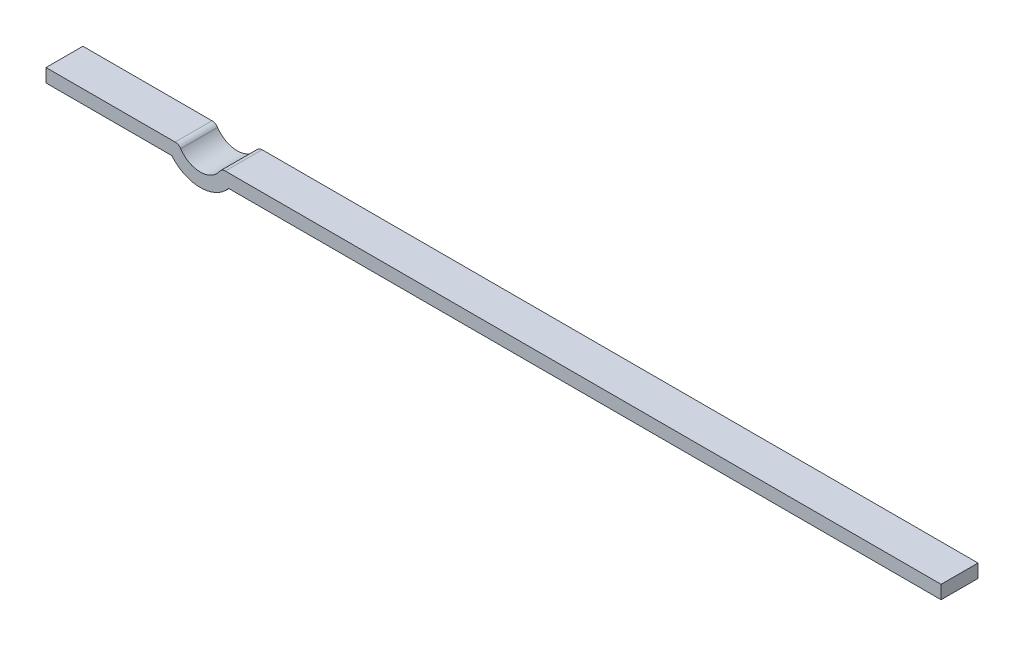
SolidWorks part; units mm, degrees
ref_plane "Plano frontal" through (0, 0, 0) normal (0, 0, 1) x (1, 0, 0)
ref_plane "Plano superior" through (0, 0, 0) normal (0, 1, 0) x (1, 0, 0)
ref_plane "Plano direito" through (0, 0, 0) normal (1, 0, 0) x (0, 0, -1)
sketch "Esboço1" plane through (0, 0, 0) normal (0, 0, 1) x (1, 0, 0)
  line L0 (-4.0006, 0.1) -> (6.675, 0.1)
  line L1 (-3.9505, -0.1) -> (6.675, -0.1)
  line L2 (-6.675, -0.1) -> (-6.675, 0.1)
  line L3 (-6.675, 0.1) -> (-4.7489, 0.1)
  line L4 (6.675, -0.1) -> (6.675, 0.1)
  line L5 (-6.675, -0.1) -> (6.675, 0.1) construction
  line L6 (-6.675, 0.1) -> (6.675, -0.1) construction
  line L7 (-6.675, -0.1) -> (-4.799, -0.1)
  arc A0 (-3.9505, -0.1) -> (-4.799, -0.1) centre (-4.3748, 0.25) cw
  arc A1 (-4.6658, 0.0556) -> (-4.0837, 0.0556) centre (-4.3748, 0.25) ccw
  arc A2 (-4.0837, 0.0556) -> (-4.0006, 0.1) centre (-4.0006, 0) cw
  arc A3 (-4.6658, 0.0556) -> (-4.7489, 0.1) centre (-4.7489, 0) ccw
  point P0 (0, 0)
  point P13 (-4.0585, 0.1)
  dimension "D5" = 0.8485
  dimension "D4" = 0.55
  dimension "D6" = 0.7
  dimension "D7" = 0.1
  dimension "D1" = 0.2
  dimension "D2" = 13.35
  dimension "D3" = 1.876
extrude "Ressalto-extrusão1" add sketch "Esboço1" along normal blind 0.55
